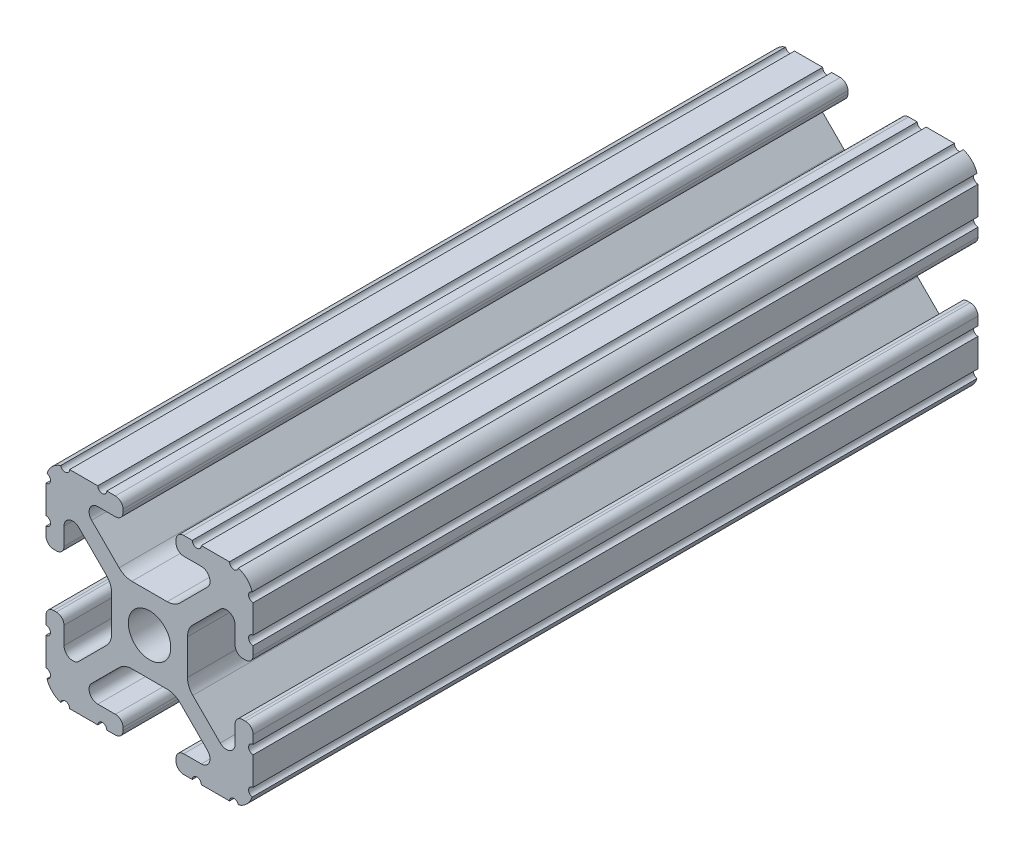
SolidWorks part; units mm, degrees
ref_plane "Front Plane" through (0, 0, 0) normal (0, 0, 1) x (1, 0, 0)
ref_plane "Top Plane" through (0, 0, 0) normal (0, 1, 0) x (1, 0, 0)
ref_plane "Right Plane" through (0, 0, 0) normal (1, 0, 0) x (0, 0, -1)
sketch "Sketch2" plane through (0, 0, 0) normal (0, 0, 1) x (1, 0, 0)
  line L0 (0, 12.7) -> (0, -12.7) construction
  line L1 (-12.7, 0) -> (12.7, 0) construction
  line L2 (3.2512, -12.7) -> (12.7, -12.7)
  line L3 (12.7, -12.7) -> (12.7, -3.2512)
  line L4 (3.2512, -12.7) -> (3.2512, -10.4902)
  line L5 (3.2512, -10.4902) -> (8.9276, -10.4902)
  line L6 (8.9276, -10.4902) -> (3.0856, -4.6482)
  line L7 (0, 0) -> (12.7, -12.7) construction
  line L8 (12.7, -3.2512) -> (10.4902, -3.2512)
  line L9 (10.4902, -3.2512) -> (10.4902, -8.9276)
  line L10 (10.4902, -8.9276) -> (4.6482, -3.0856)
  circle A0 centre (0, 0) radius 2.6035
  arc A1 (6.3485, -10.4902) -> (7.1039, -8.6665) centre (6.3485, -9.4219) ccw construction
  point P8 (0, -4.6482)
  dimension "Center Hole Diameter" = 5.207
  dimension "Rail Height" = 25.4
  dimension "Rail Width" = 25.4
  dimension "T-Slot Width" = 6.5024
  dimension "Slot Inner Width" = 14.8336
  dimension "Thickness" = 2.2098
  dimension "Slot Depth" = 5.842
  dimension "D1" = 2.2098
sketch "Sketch3" plane through (0, 0, 0) normal (1, 0, 0) x (0, 0, -1)
  line L0 (-63.5, -12.7) -> (63.5, -12.7) construction
  line L1 (-57.15, 0) -> (57.15, 0) construction
  dimension "Length" = 127
  dimension "D1" = 114.3
sketch "Sketch4" plane through (0, 0, 0) normal (0, 0, 1) x (1, 0, 0)
  line L0 (4.1904, -12.7) -> (10.1173, -12.7)
  line L1 (3.2512, -12.7) -> (12.7, -12.7) construction
  line L2 (3.2512, -12.7) -> (3.2512, -10.4902) construction
  line L3 (3.2512, -10.4902) -> (8.9276, -10.4902) construction
  line L4 (3.2512, -11.4294) -> (3.2512, -11.7608)
  line L5 (4.1904, -10.4902) -> (6.3485, -10.4902)
  line L6 (0, -4.6482) -> (2.164, -4.6482)
  line L7 (8.9276, -10.4902) -> (3.0856, -4.6482) construction
  line L8 (3.7373, -5.2999) -> (7.1039, -8.6665)
  line L9 (12.7, -12.7) -> (12.7, -3.2512) construction
  line L10 (10.4902, -8.9276) -> (4.6482, -3.0856) construction
  line L11 (10.4902, -3.2512) -> (10.4902, -8.9276) construction
  line L12 (10.4902, -6.3485) -> (10.4902, -4.1904)
  line L13 (12.7, -3.2512) -> (10.4902, -3.2512) construction
  line L14 (11.4294, -3.2512) -> (11.7608, -3.2512)
  line L15 (12.7, -4.1904) -> (12.7, -10.1173)
  line L16 (8.6665, -7.1039) -> (5.2999, -3.7373)
  line L17 (4.6482, 0) -> (4.6482, -2.164)
  line L18 (-12.7, 0) -> (12.7, 0) construction
  line L19 (0, -4.6482) -> (0, -2.6035)
  line L20 (0, 12.7) -> (0, -12.7) construction
  line L21 (4.6482, 0) -> (2.6035, 0)
  arc A0 (3.2512, -11.7608) -> (4.1904, -12.7) centre (4.1904, -11.7608) ccw
  arc A2 (3.2512, -11.4294) -> (4.1904, -10.4902) centre (4.1904, -11.4294) cw
  arc A3 (6.3485, -10.4902) -> (7.1039, -8.6665) centre (6.3485, -9.4219) ccw
  arc A4 (2.164, -4.6482) -> (3.7373, -5.2999) centre (2.164, -6.8732) cw
  arc A5 (10.1173, -12.7) -> (12.7, -10.1173) centre (10.1173, -10.1173) ccw
  arc A6 (8.6665, -7.1039) -> (10.4902, -6.3485) centre (9.4219, -6.3485) ccw
  arc A7 (10.4902, -4.1904) -> (11.4294, -3.2512) centre (11.4294, -4.1904) cw
  arc A8 (11.7608, -3.2512) -> (12.7, -4.1904) centre (11.7608, -4.1904) cw
  arc A9 (5.2999, -3.7373) -> (4.6482, -2.164) centre (6.8732, -2.164) cw
  circle A10 centre (0, 0) radius 2.6035 construction
  arc A11 (0, -2.6035) -> (2.6035, 0) centre (0, 0) ccw
  dimension "D1" = 2.5827
  dimension "D2" = 2.225
  dimension "D3" = 0.9392
extrude "Boss-Extrude1" add sketch "Sketch4" along normal mid plane 127
sketch "Sketch5" plane through (0, 0, 0) normal (0, 0, 1) x (1, 0, 0)
  line L0 (3.2512, -12.7) -> (12.7, -12.7) construction
  line L1 (4.1904, -10.4902) -> (6.3485, -10.4902) construction
  line L3 (0, 0) -> (12.7, -12.7) construction
  line L4 (6.3485, -10.4902) -> (6.3485, -12.7) construction
  line L5 (8.9276, -10.4902) -> (3.0856, -4.6482) construction
  circle A0 centre (10.3562, -12.7) radius 0.5524
  circle A1 centre (5.796, -12.7) radius 0.5524
  circle A2 centre (12.7, -10.3562) radius 0.5524
  circle A3 centre (12.7, -5.796) radius 0.5524
  point P10 (5.2694, -10.4902)
  point P12 (9.4219, -6.3485)
  dimension "D1" = 1.1049
extrude "Cut-Extrude1" cut sketch "Sketch5" against normal through all both and the other way through all
mirror "Mirror1" about plane through (0, 0, 0) normal (1, 0, 0) of bodies 137 134
mirror "Mirror2" about plane through (0, 0, 0) normal (0, 1, 0) of bodies 135
sketch "Sketch7" plane through (0, 0, 0) normal (0, 1, 0) x (1, 0, 0)
  line L0 (12.7, -63.5) -> (12.7, 63.5) construction
  line L1 (-12.7, -63.5) -> (12.7, -63.5)
  line L2 (-12.7, -63.5) -> (-12.7, -25.4)
  line L3 (-12.7, -25.4) -> (12.7, -25.4)
  line L4 (12.7, -63.5) -> (12.7, -25.4)
  dimension "D1" = 38.1
extrude "Cut-Extrude2" cut sketch "Sketch7" against normal mid plane 25.4
equation "\"D1@Boss-Extrude1\"=\"Length@Sketch3\""
equation "\"D1@Sketch2\"=\"Thickness@Sketch2\""
equation "\"D2@Sketch4\"=\"Slot Inner Width@Sketch2\"*0.15"
equation "\"D1@Sketch4\"=\"D3@Sketch4\"*2.75"
equation "\"D3@Sketch4\"=\"Thickness@Sketch2\"*0.425"
equation "\"D1@Sketch5\"=\"Thickness@Sketch2\"*0.5"
equation "\"D1@Sketch3\"=\"Length@Sketch3\"*0.9"
